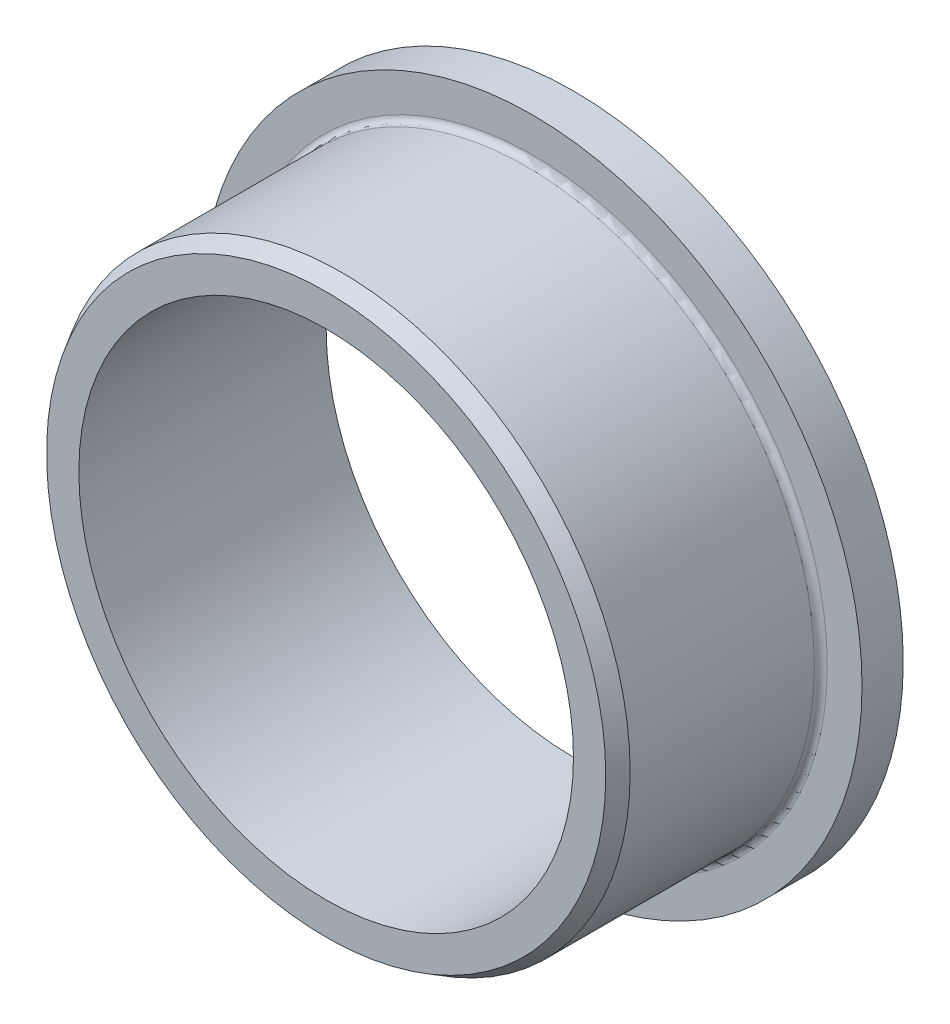
SolidWorks part; units mm, degrees
material "PVC Rigid"
ref_plane "Front Plane" through (0, 0, 0) normal (0, 0, 1) x (1, 0, 0)
ref_plane "Top Plane" through (0, 0, 0) normal (0, 1, 0) x (1, 0, 0)
ref_plane "Right Plane" through (0, 0, 0) normal (1, 0, 0) x (0, 0, -1)
sketch "Sketch1" plane through (0, 0, 0) normal (0, 1, 0) x (1, 0, 0)
  line L0 (25.4, 0) -> (19.05, 0)
  line L1 (19.05, 0) -> (19.05, -19.05)
  line L2 (19.05, -19.05) -> (21.5358, -19.05)
  line L3 (21.5358, -19.05) -> (22.225, -17.8562)
  line L4 (22.225, -17.8562) -> (22.225, -3.675)
  line L5 (22.725, -3.175) -> (25.4, -3.175)
  line L6 (25.4, -3.175) -> (25.4, 0)
  line L7 (0, 0) -> (0, -19.05) construction
  arc A0 (22.225, -3.675) -> (22.725, -3.175) centre (22.725, -3.675) cw
  dimension "D7" = 0.5
  dimension "D1" = 19.05
  dimension "D2" = 50.8
  dimension "D3" = 38.1
  dimension "D4" = 44.45
  dimension "D5" = 3.175
  dimension "D6" = 60
  dimension "D8" = 1.1938
revolve "Revolve1" add sketch "Sketch1" angle 360 about L7
